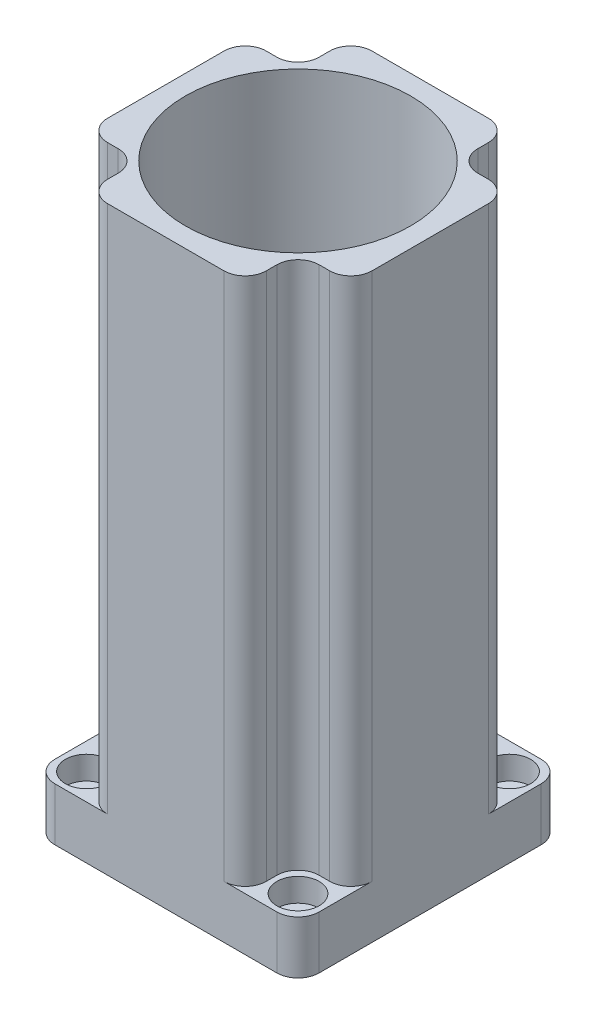
SolidWorks part; units mm, degrees
ref_plane "Plan de face" through (0, 0, 0) normal (0, 0, 1) x (1, 0, 0)
ref_plane "Plan de dessus" through (0, 0, 0) normal (0, 1, 0) x (1, 0, 0)
ref_plane "Plan de droite" through (0, 0, 0) normal (1, 0, 0) x (0, 0, -1)
sketch "Esquisse1" plane through (0, 0, 0) normal (0, 1, 0) x (1, 0, 0)
  line L0 (0, 50) -> (50, 0) construction
  line L1 (0, 0) -> (50, 0)
  line L2 (0, 0) -> (0, 50)
  line L3 (0, 50) -> (50, 50)
  line L4 (50, 0) -> (50, 50)
  circle A0 centre (25, 25) radius 14.5
  dimension "D3" = 29
  dimension "D1" = 50
  dimension "D2" = 50
extrude "Boss.-Extru.1" add sketch "Esquisse1" along normal blind 10
sketch "Esquisse2" plane through (0, 10, 0) normal (0, 1, 0) x (1, 0, 0)
  line L0 (25, 46.3) -> (25, 3.7) construction
  line L4 (40, 46) -> (40, 44)
  line L5 (0, 50) -> (10, 50)
  line L6 (0, 50) -> (0, 40)
  line L7 (4, 40) -> (6, 40)
  line L13 (3.7, 25) -> (50003.7, 25) construction
  line L14 (10, 46) -> (10, 44)
  line L15 (46, 40) -> (44, 40)
  line L16 (46, 10) -> (44, 10)
  line L17 (40, 4) -> (40, 6)
  line L18 (0, 50) -> (0, 0)
  line L19 (0, 0) -> (50, 0)
  line L20 (50, 0) -> (50, 50)
  line L21 (50, 50) -> (0, 50)
  line L22 (0, 36) -> (0, 0)
  line L23 (0, 0) -> (50, 0)
  line L24 (50, 0) -> (50, 50)
  line L25 (50, 50) -> (14, 50)
  line L26 (10, 4) -> (10, 6)
  line L27 (4, 10) -> (6, 10)
  circle A0 centre (25, 25) radius 14.5 construction
  circle A1 centre (25, 25) radius 14.5
  circle A3 centre (25, 25) radius 21.3
  arc A7 (14, 50) -> (10, 46) centre (14, 46) ccw
  arc A8 (10, 44) -> (6, 40) centre (6, 44) cw
  arc A9 (4, 40) -> (0, 36) centre (4, 36) ccw
  arc A10 (36, 50) -> (40, 46) centre (36, 46) cw
  arc A11 (40, 44) -> (44, 40) centre (44, 44) ccw
  arc A12 (46, 40) -> (50, 36) centre (46, 36) cw
  arc A13 (46, 10) -> (50, 14) centre (46, 14) ccw
  arc A14 (40, 6) -> (44, 10) centre (44, 6) cw
  arc A15 (36, 0) -> (40, 4) centre (36, 4) ccw
  arc A16 (14, 0) -> (10, 4) centre (14, 4) cw
  arc A17 (10, 6) -> (6, 10) centre (6, 6) ccw
  arc A18 (4, 10) -> (0, 14) centre (4, 14) cw
  point P17 (10, 40)
  dimension "D2" = 42.6
  dimension "D3" = 14
  dimension "D4" = 4
  dimension "D5" = 14
  dimension "D1" = 0
extrude "Boss.-Extru.2" add sketch "Esquisse2" along normal blind 100
sketch "Esquisse8" plane through (0, 0, 0) normal (0, 1, 0) x (1, 0, 0)
  circle A0 centre (25, 25) radius 17.5
  circle A1 centre (25, 25) radius 21.3
  circle A2 centre (25, 25) radius 21.3
  point P1 (25, 42.5)
  point P5 (42.5, 25)
  point P6 (25, 7.5)
  point P7 (7.5, 25)
  dimension "D2" = 35
  dimension "D1" = 0
sketch "Esquisse5" plane through (0, 10, 0) normal (0, 1, 0) x (1, 0, 0)
  line L1 (5, 45) -> (45, 45)
  line L2 (5, 45) -> (5, 5)
  line L3 (5, 5) -> (45, 5)
  line L4 (45, 45) -> (45, 5)
  line L5 (5, 45) -> (45, 5) construction
  line L6 (5, 5) -> (45, 45) construction
  line L7 (0, 0) -> (14, 0) construction
  line L8 (50, 14) -> (50, 36) construction
  circle A0 centre (25, 25) radius 14.5 construction
  circle A1 centre (25, 25) radius 14.5
  dimension "D1" = 5
  dimension "D2" = 5
hole_wizard "Chambrage pour vis à six pans creux M41" positions "Esquisse3D2" profile "Esquisse7" counterbore size "M4" standard "ISO" end condition through all
sketch3d "Esquisse3D2"
  point P0 (5, 10, -45)
  point P3 (45, 10, -45)
  point P6 (45, 10, -5)
  point P9 (5, 10, -5)
sketch "Esquisse7" plane through (5, 10, -45) normal (1, 0, 0) x (0, 0, 1)
  line L0 (0, 0) -> (0, 10)
  line L1 (0, 10) -> (2.25, 10)
  line L3 (2.25, 10) -> (2.25, 4.4)
  line L4 (2.25, 4.4) -> (4, 4.4)
  line L5 (4, 4.4) -> (4, 0)
  line L7 (4, 0) -> (0, 0)
  line L11 (0, -6.35) -> (0, 107.95) construction
  dimension "Diamètre du perçage jusqu'au prochain" = 4.5
  dimension "Profondeur du perçage jusqu'au prochain" = 10
  dimension "Diamètre du chambrage" = 8
  dimension "Profondeur du chambrage" = 4.4
hole_wizard "Chambrage pour vis à six pans creux M42" positions "Esquisse3D4" profile "Esquisse10" counterbore size "M4" standard "ISO" end condition through all
sketch3d "Esquisse3D4"
  point P0 (25, 0, -7.5)
  point P3 (42.5, 0, -25)
  point P6 (25, 0, -42.5)
  point P9 (7.5, 0, -25)
sketch "Esquisse10" plane through (25, 0, -7.5) normal (1, 0, 0) x (0, 0, -1)
  line L0 (0, 0) -> (0, 110)
  line L1 (0, 110) -> (2.4, 110)
  line L3 (2.4, 110) -> (2.4, 4.4)
  line L4 (2.4, 4.4) -> (4, 4.4)
  line L5 (4, 4.4) -> (4, 0)
  line L7 (4, 0) -> (0, 0)
  line L11 (0, -6.35) -> (0, 107.95) construction
  dimension "Diamètre du perçage jusqu'au prochain" = 4.8
  dimension "Profondeur du perçage jusqu'au prochain" = 110
  dimension "Diamètre du chambrage" = 8
  dimension "Profondeur du chambrage" = 4.4
fillet "Congé1" radius 4 4 edges at (50, 5, -50) (0, 5, -50) (50, 5, 0) (0, 5, 0)
